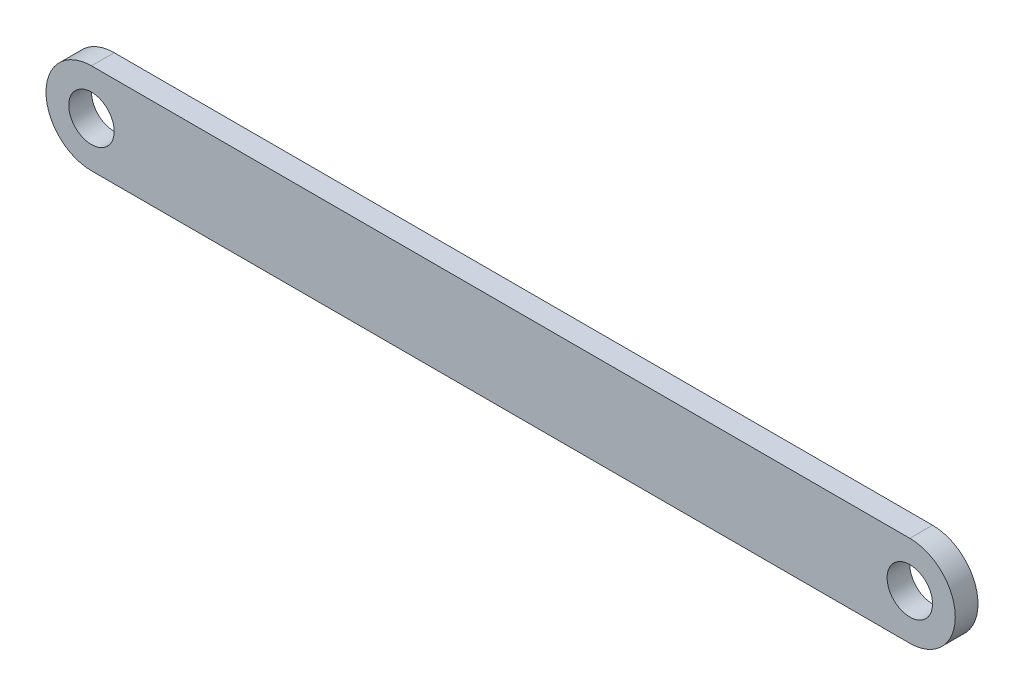
SolidWorks part; units mm, degrees
ref_plane "Front Plane" through (0, 0, 0) normal (0, 0, 1) x (1, 0, 0)
ref_plane "Top Plane" through (0, 0, 0) normal (0, 1, 0) x (1, 0, 0)
ref_plane "Right Plane" through (0, 0, 0) normal (1, 0, 0) x (0, 0, -1)
sketch "Sketch1" plane through (0, 0, 0) normal (0, 0, 1) x (1, 0, 0)
  line L0 (-57.15, 0) -> (57.15, 0) construction
  line L1 (-57.15, 6.35) -> (57.15, 6.35)
  line L2 (-57.15, -6.35) -> (57.15, -6.35)
  arc A0 (-57.15, 6.35) -> (-57.15, -6.35) centre (-57.15, 0) ccw
  arc A1 (57.15, -6.35) -> (57.15, 6.35) centre (57.15, 0) ccw
  circle A2 centre (-57.15, 0) radius 3.175
  circle A3 centre (57.15, 0) radius 3.175
  point P2 (0, 0)
  dimension "D3" = 6.35
  dimension "D1" = 12.7
  dimension "D2" = 114.3
extrude "Boss-Extrude2" add sketch "Sketch1" along normal blind 3.175 contours L2 A1 L1 A0 | A2 | A3
